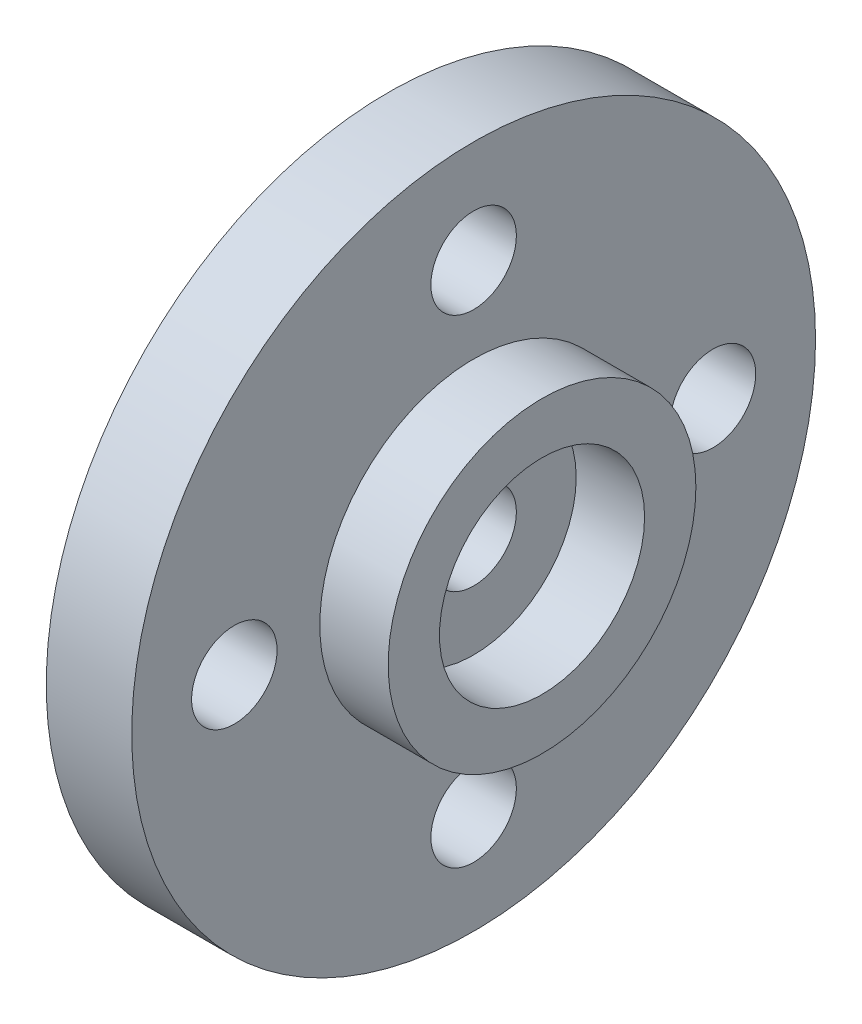
SolidWorks part; units mm, degrees
ref_plane "前视基准面" through (0, 0, 0) normal (0, 0, 1) x (1, 0, 0)
ref_plane "上视基准面" through (0, 0, 0) normal (0, 1, 0) x (1, 0, 0)
ref_plane "右视基准面" through (0, 0, 0) normal (1, 0, 0) x (0, 0, -1)
other "Configuration Table"
sketch "草图1" plane through (0, 0, 0) normal (1, 0, 0) x (0, 0, -1)
  circle A0 centre (0, 0) radius 10
  dimension "D1" = 20
extrude "凸台-拉伸1" add sketch "草图1" along normal blind 2.5 contours A0
sketch "草图2" plane through (2.5, 0, 0) normal (1, 0, 0) x (0, 0, -1)
  circle A0 centre (0, 0) radius 4.5
  circle A1 centre (0, 0) radius 3
  dimension "D1" = 6
  dimension "D2" = 9
extrude "凸台-拉伸2" add sketch "草图2" along normal blind 2
hole_wizard "M3 螺纹孔1" positions "草图3" profile "草图4" tap size "M3" standard "GB" end condition through all
sketch "草图3" plane through (0, 0, 0) normal (-1, 0, 0) x (0, 0, 1)
  circle A0 centre (0, 0) radius 7
  point P0 (0, 0)
  point P7 (0, 7)
  point P9 (-7, 0)
  point P11 (7, 0)
  point P13 (0, -7)
  dimension "D1" = 14
sketch "草图4" plane through (0, 0, 0) normal (0, 1, 0) x (0, 0, 1)
  line L0 (0, 0) -> (0, 4.5)
  line L1 (0, 4.5) -> (1.25, 4.5)
  line L2 (1.25, 4.5) -> (1.25, 0)
  line L5 (1.25, 0) -> (0, 0)
  line L11 (0, -6.35) -> (0, 107.95) construction
  dimension "通孔螺纹孔钻头直径" = 2.5
  dimension "通孔螺纹孔钻头深度" = 4.5
cosmetic thread "孔螺蚊线1" parameters "D2"=3
cosmetic thread "孔螺蚊线2" parameters "D2"=3
cosmetic thread "孔螺蚊线3" parameters "D2"=3
cosmetic thread "孔螺蚊线4" parameters "D2"=3
cosmetic thread "孔螺蚊线5" parameters "D2"=3
